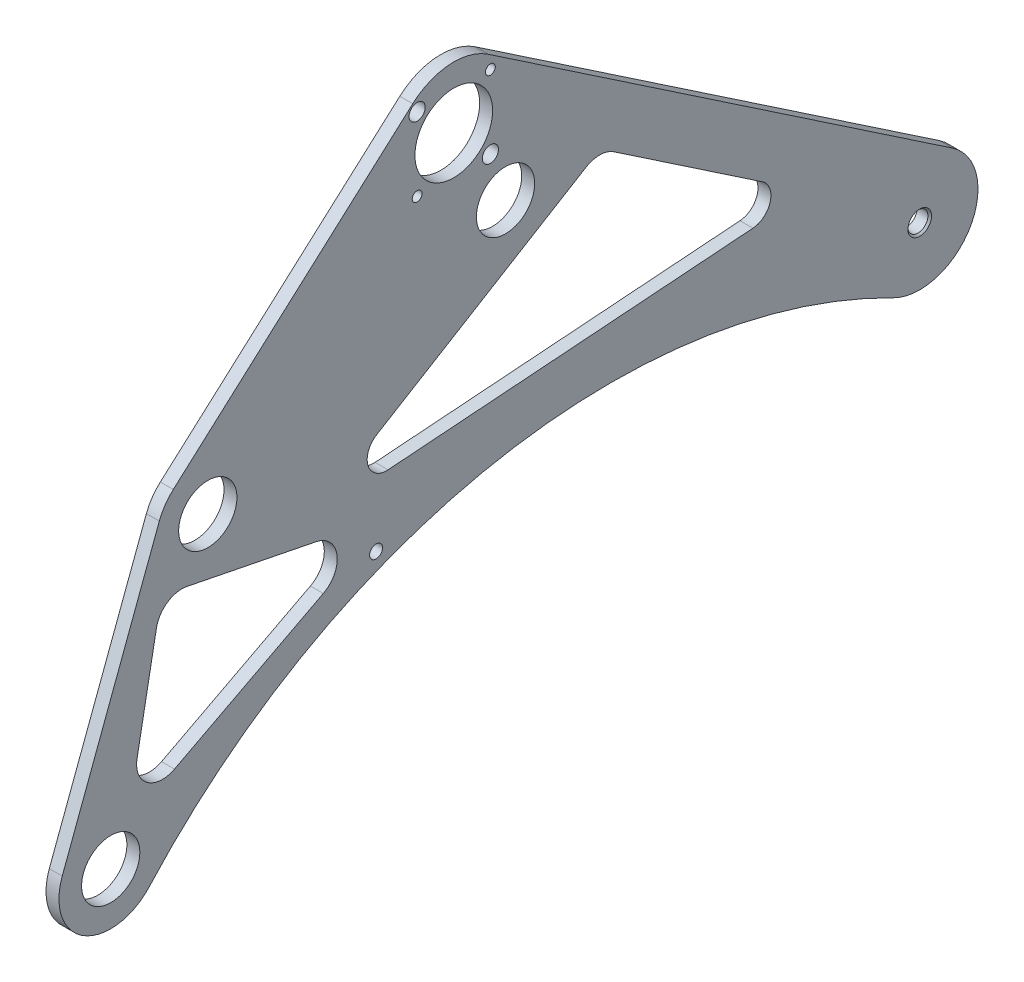
SolidWorks part; units mm, degrees
material "Acrylic (Medium-high impact)"
ref_plane "Front Plane" through (0, 0, 0) normal (0, 0, 1) x (1, 0, 0)
ref_plane "Top Plane" through (0, 0, 0) normal (0, 1, 0) x (1, 0, 0)
ref_plane "Right Plane" through (0, 0, 0) normal (1, 0, 0) x (0, 0, -1)
sketch "Sketch1" plane through (0, 0, 0) normal (1, 0, 0) x (0, 0, -1)
  line L0 (-548.7618, -304.8) -> (152.435, -304.8)
  line L1 (-192.8252, -101.6) -> (-152.4, -101.6)
  line L2 (-234.95, -143.7248) -> (-234.95, -186.4752)
  line L3 (-192.8252, -228.6) -> (-152.4, -228.6)
  line L4 (-152.4, -101.6) -> (-152.4, -228.6)
  line L10 (-225.1934, 154.4964) -> (-199.7934, 113.2214)
  line L11 (-200.4191, 108.2498) -> (-394.0941, -79.0752)
  line L12 (-400.6203, -74.7955) -> (-352.9953, 52.2045)
  line L13 (-350.2484, 54.6734) -> (-296.1816, 68.6089)
  line L14 (-293.9553, 70.1155) -> (-231.8247, 154.7668)
  circle A1 centre (0, 0) radius 6.35
  circle A6 centre (-396.875, -76.2) radius 9.525
  circle A7 centre (-349.25, 50.8) radius 9.525
  circle A8 centre (-203.2, 111.125) radius 9.525
  arc A9 (-234.95, -186.4752) -> (-192.8252, -228.6) centre (-192.8252, -186.4752) ccw
  arc A10 (-192.8252, -101.6) -> (-234.95, -143.7248) centre (-192.8252, -143.7248) ccw
  circle A11 centre (-230.9942, 0) radius 120.65
  circle A12 centre (-228.6, 152.4) radius 29.845
  arc A23 (-231.8247, 154.7668) -> (-225.1934, 154.4964) centre (-228.6, 152.4) cw
  arc A24 (-199.7934, 113.2214) -> (-200.4191, 108.2498) centre (-203.2, 111.125) cw
  arc A25 (-394.0941, -79.0752) -> (-400.6203, -74.7955) centre (-396.875, -76.2) cw
  arc A26 (-352.9953, 52.2045) -> (-350.2484, 54.6734) centre (-349.25, 50.8) cw
  arc A27 (-296.1816, 68.6089) -> (-293.9553, 70.1155) centre (-297.18, 72.4823) ccw
  circle B0 centre (-349.25, 50.8) radius 4
  line B1 (-396.875, -76.2) -> (-382.9261, -60.8997)
  circle B2 centre (-396.875, -76.2) radius 4
  circle B3 centre (-203.2, 111.125) radius 4
  line B4 (-228.6, 152.4) -> (-225.2662, 168.6097)
  circle B5 centre (-228.6, 152.4) radius 4
  circle B6 centre (-297.18, 72.4823) radius 4
  dimension "D1" = 12.7
  dimension "D2" = 19.05
  dimension "D3" = 42.1248
  dimension "D4" = 127
  dimension "D7" = 203.2
  dimension "D6" = 241.3
  dimension "D16" = 59.69
  dimension "D5" = 82.55
  dimension "D8" = 304.8
  dimension "D9" = 152.4
  dimension "D10" = 396.875
  dimension "D11" = 76.2
  dimension "D12" = 349.25
  dimension "D13" = 50.8
  dimension "D14" = 203.2
  dimension "D15" = 111.125
  dimension "D17" = 228.6
  dimension "D18" = 152.4
  dimension "D23" = 297.18
sketch_block_instance "Block1-1"
sketch_block "Block1"
sketch_block_instance "Block2-1"
sketch_block "Block2"
sketch_block_instance "Block3-1"
sketch_block "Block3"
sketch_block_instance "Block4-1"
sketch_block "Block4" parameters "D1"=8
sketch_block_instance "Block5-1"
sketch_block "Block5"
other "Belt1"
sketch "Sketch2" plane through (0, 0, 0) normal (1, 0, 0) x (0, 0, -1)
  line L1 (-420.6578, -67.2815) -> (-373.0328, 59.7185)
  line L3 (-366.1902, 69.7259) -> (-248.7165, 174.8745)
  line L5 (-211.7241, 177.3996) -> (15.9877, 23.6839)
  line L6 (-1001.8623, -101.6) -> (216.545, -101.6) construction
  line L7 (-1029.8132, 182.5625) -> (188.5941, 182.5625) construction
  arc A0 (-366.1902, 69.7259) -> (-373.0328, 59.7185) centre (-349.25, 50.8) ccw
  arc A2 (-420.6578, -67.2815) -> (-377.9906, -93.1865) centre (-396.875, -76.2) ccw
  arc A4 (-211.7241, 177.3996) -> (-248.7165, 174.8745) centre (-228.6, 152.4) ccw
  arc A5 (-12.9753, -25.4592) -> (15.9877, 23.6839) centre (0, 0) ccw
  arc A8 (-377.9906, -93.1865) -> (-12.9753, -25.4592) centre (-151.3783, -297.0244) cw
  circle A12 centre (-396.875, -76.2) radius 9.525 construction
  circle A13 centre (-349.25, 50.8) radius 9.525 construction
  dimension "D1" = 25.4
  dimension "D2" = 57.15
  dimension "D3" = 60.325
  dimension "D4" = 304.8
  dimension "D6" = 284.1625
extrude "Boss-Extrude1" add sketch "Sketch2" along normal blind 6.35
sketch "Sketch3" plane through (6.35, 0, 0) normal (1, 0, 0) x (0, 0, -1)
  line L0 (-210.6395, 170.3605) -> (-246.5605, 134.4395) construction
  line L1 (-228.6, 152.4) -> (-228.6, 205.0182) construction
  line L2 (-246.5605, 170.3605) -> (-210.6395, 134.4395) construction
  circle A0 centre (-203.2, 111.125) radius 14.2875
  circle A1 centre (-349.25, 50.8) radius 14.2875
  circle A2 centre (-396.875, -76.2) radius 14.2875
  circle A3 centre (-228.6, 152.4) radius 19.05
  circle A5 centre (-246.5605, 134.4395) radius 2.413
  circle A7 centre (-210.6395, 134.4395) radius 3.9687
  circle A8 centre (-210.6395, 170.3605) radius 2.413
  circle A9 centre (-246.5605, 170.3605) radius 3.9687
  point P18 (-228.6, 152.4)
  point P28 (-228.6, 152.4)
  dimension "D1" = 38.1
  dimension "D2" = 28.575
  dimension "D3" = 4.826
  dimension "D4" = 50.8
  dimension "D5" = 45
  dimension "D6" = 7.9375
  dimension "D7" = 50.8
extrude "Cut-Extrude1" cut sketch "Sketch3" against normal up to next
hole_wizard "3/8 Clearance Hole2" positions "Sketch7" profile "Sketch8" hole size "3/8" standard "ANSI Inch" end condition through all
sketch "Sketch7" plane through (6.35, 0, 0) normal (1, 0, 0) x (0, 0, -1)
  point P0 (0, 0)
sketch "Sketch8" plane through (6.35, 0, 0) normal (0, 1, 0) x (0, 0, -1)
  line L0 (0, 0) -> (0, 6.35)
  line L1 (0, 6.35) -> (4.9022, 6.35)
  line L2 (4.9022, 6.35) -> (4.9022, 0.8915)
  line L3 (4.9022, 0.8915) -> (5.7937, 0)
  line L5 (5.7937, 0) -> (0, 0)
  line L6 (-4.9022, 0.8915) -> (-5.7937, 0) construction
  line L11 (0, -6.35) -> (0, 107.95) construction
  dimension "Thru Hole Dia." = 9.8044
  dimension "Thru Hole Depth" = 6.35
  dimension "Near C'Sink Dia." = 11.5875
  dimension "Near C'Sink Angle" = 90
sketch "Sketch9" plane through (6.35, 0, 0) normal (1, 0, 0) x (0, 0, -1)
  line L0 (-495.9857, -101.6) -> (27.4607, -101.6) construction
  line L1 (100.4878, 182.5625) -> (-422.9585, 182.5625) construction
  arc A0 (-211.7241, 177.3996) -> (-248.7165, 174.8745) centre (-228.6, 152.4) ccw construction
  arc A1 (-420.6578, -67.2815) -> (-377.9906, -93.1865) centre (-396.875, -76.2) ccw construction
  dimension "D1" = 284.1625
hole_wizard "1/4 (0.2500) Dowel Hole2" positions "Sketch12" profile "Sketch13" hole size "1/4" standard "ANSI Inch" end condition through all
sketch "Sketch12" plane through (6.35, 0, 0) normal (1, 0, 0) x (0, 0, -1)
  point P0 (-266.7, -6.35)
  dimension "D1" = 266.7
sketch "Sketch13" plane through (6.35, -6.35, 266.7) normal (0, 1, 0) x (0, 0, -1)
  line L0 (0, 0) -> (0, 6.35)
  line L1 (0, 6.35) -> (3.175, 6.35)
  line L2 (3.175, 6.35) -> (3.175, 0)
  line L5 (3.175, 0) -> (0, 0)
  line L11 (0, -6.35) -> (0, 107.95) construction
  dimension "Thru Hole Dia." = 6.35
  dimension "Thru Hole Depth" = 6.35
sketch "Sketch14" plane through (6.35, 0, 0) normal (1, 0, 0) x (0, 0, -1)
  line L0 (-365.6004, -49.3596) -> (-292.5754, -11.2596)
  line L1 (-295.9593, 12.4534) -> (-359.4593, 25.1534)
  line L2 (-374.4325, 15.0405) -> (-383.9575, -35.7595)
  line L3 (-77.2075, 55.9493) -> (-149.9685, 105.0662)
  line L4 (-163.6599, 105.3991) -> (-266.4749, 43.0436)
  line L6 (-260.8375, 25.4) -> (-81.8386, 38.5553)
  line L9 (15.9877, 23.6839) -> (-211.7241, 177.3996) construction
  arc A0 (-383.9575, -35.7595) -> (-365.6004, -49.3596) centre (-371.475, -38.1) ccw
  arc A1 (-292.5754, -11.2596) -> (-295.9593, 12.4534) centre (-298.45, 0) ccw
  arc A2 (-359.4593, 25.1534) -> (-374.4325, 15.0405) centre (-361.95, 12.7) ccw
  circle A3 centre (-396.875, -76.2) radius 14.2875 construction
  circle A4 centre (-349.25, 50.8) radius 14.2875 construction
  circle A5 centre (-266.7, -6.35) radius 3.175 construction
  arc A9 (-149.9685, 105.0662) -> (-163.6599, 105.3991) centre (-157.0742, 94.5401) ccw
  arc A13 (-260.8375, 25.4) -> (-266.4749, 43.0436) centre (-261.5356, 34.8994) cw
  circle A15 centre (-203.2, 111.125) radius 14.2875 construction
  arc A21 (-81.8386, 38.5553) -> (-77.2075, 55.9493) centre (-82.5367, 48.0546) ccw
  point P21 (0, 0)
  point P44 (-288.2635, 17.3613)
  dimension "D1" = 38.1
  dimension "D2" = 25.4
  dimension "D3" = 25.4
  dimension "D4" = 38.1
  dimension "D5" = 12.7
  dimension "D6" = 31.75
  dimension "D7" = 6.35
  dimension "D8" = 25.4
  dimension "D9" = 25.4
  dimension "D12" = 9.525
  dimension "D13" = 25.4
  dimension "D14" = 12.7
  dimension "D15" = 44.45
  dimension "D16" = 50.8
  dimension "D11" = 9.525
  dimension "D10" = 25.4
extrude "Cut-Extrude2" cut sketch "Sketch14" against normal through all
